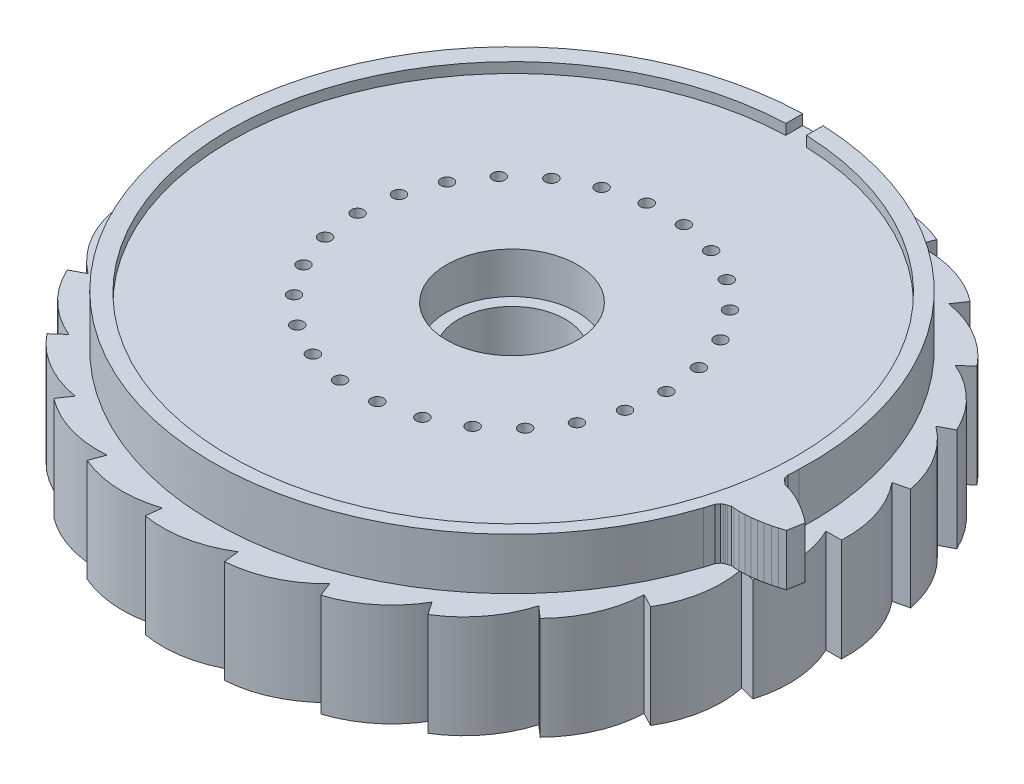
SolidWorks part; units mm, degrees
material "1060 Alloy"
ref_plane "Front Plane" through (0, 0, 0) normal (0, 0, 1) x (1, 0, 0)
ref_plane "Top Plane" through (0, 0, 0) normal (0, 1, 0) x (1, 0, 0)
ref_plane "Right Plane" through (0, 0, 0) normal (1, 0, 0) x (0, 0, -1)
sketch "Sketch1" plane through (0, 0, 0) normal (0, 1, 0) x (1, 0, 0)
  line L0 (0, 0) -> (54.8903, 0) construction
  line L1 (0, 0) -> (47.5263, 11.7142) construction
  line L2 (0, 0) -> (29.6137, 7.2991)
  line L3 (0, 0) -> (32, 0)
  circle A0 centre (0, 0) radius 32 construction
  circle A1 centre (0, 0) radius 30.5 construction
  arc A2 (29.6137, 7.2991) -> (32, 0) centre (21.3514, 0.5583) cw
  circle A3 centre (0, 0) radius 31.25 construction
  dimension "D1" = 62.5
  dimension "D2" = 1.5
  dimension "D4" = 0.75
  dimension "D3" = 13.846
extrude "Extrude ratchet edge" add sketch "Sketch1" along normal blind 10
pattern_circular "Pattern edge to form gear" count 26 over 360 about axis through (0, 0, 0) along (0, 1, 0) of "Extrude ratchet edge"
sketch "Sketch12" plane through (0, 10, 0) normal (0, 1, 0) x (1, 0, 0)
  line L0 (28.9274, -2.1257) -> (29.0264, -2.5152)
  line L1 (29.0264, -2.5152) -> (29.1427, -2.6718)
  line L2 (29.1427, -2.6718) -> (29.2623, -2.7873)
  line L3 (29.2623, -2.7873) -> (29.3837, -2.8801)
  line L4 (29.3837, -2.8801) -> (29.6242, -3.0821)
  line L5 (29.6242, -3.0821) -> (29.8792, -3.1399)
  line L6 (29.8792, -3.1399) -> (30.3843, -3.2992)
  line L7 (30.3843, -3.2992) -> (30.8844, -3.4996)
  line L8 (30.8844, -3.4996) -> (31.3799, -3.7334)
  line L9 (31.3799, -3.7334) -> (31.8708, -3.9966)
  line L10 (31.8708, -3.9966) -> (32.3568, -4.2867)
  line L11 (32.3568, -4.2867) -> (32.8378, -4.602)
  line L12 (32.8378, -4.602) -> (33.3134, -4.9413)
  line L13 (33.3134, -4.9413) -> (33.7833, -5.3035)
  line L14 (33.7833, -5.3035) -> (33.502, -6.8593)
  line L15 (33.502, -6.8593) -> (32.9351, -7.0341)
  line L16 (32.9351, -7.0341) -> (32.3708, -7.1854)
  line L17 (32.3708, -7.1854) -> (31.8099, -7.3124)
  line L18 (31.8099, -7.3124) -> (31.253, -7.414)
  line L19 (31.253, -7.414) -> (30.7011, -7.4887)
  line L20 (30.7011, -7.4887) -> (30.1551, -7.5342)
  line L21 (30.1551, -7.5342) -> (29.6165, -7.5468)
  line L22 (29.6165, -7.5468) -> (29.0876, -7.5192)
  line L23 (29.0876, -7.5192) -> (28.8285, -7.4842)
  line L24 (28.8285, -7.4842) -> (28.5325, -7.5891)
  line L25 (28.5325, -7.5891) -> (28.3863, -7.6336)
  line L26 (28.3863, -7.6336) -> (28.2339, -7.6999)
  line L27 (28.2339, -7.6999) -> (28.07, -7.8059)
  line L28 (28.07, -7.8059) -> (27.841, -8.136)
  line L29 (27.841, -8.136) -> (27.578, -8.987)
  line L779 (28.9844, -1.1053) -> (28.9274, -2.1257)
  arc A0 (27.578, -8.987) -> (28.9844, -1.1053) centre (0, 0) cw
extrude "Gear face" add sketch "Sketch12" along normal blind 5
sketch "Sketch7" plane through (0, 15, 0) normal (0, 1, 0) x (1, 0, 0)
  circle A0 centre (0, 0) radius 6.35
  dimension "D1" = 12.7
sketch "Sketch10" plane through (0, 15, 0) normal (0, 1, 0) x (1, 0, 0)
  line L0 (-0.7538, 29.3517) -> (-0.7538, 27.3517)
  line L1 (1.2462, 27.3517) -> (1.2462, 29.3517)
  line L2 (1.2462, 29.3517) -> (-0.7538, 29.3517)
  line L3 (0.2462, -0.1301) -> (0.2462, 41.1735) construction
  line L4 (0.2462, -0.1301) -> (0.2462, 36.6199) construction
  arc A0 (-0.7538, 27.3517) -> (1.2462, 27.3517) centre (0.2462, -0.1301) ccw
  dimension "D1" = 2
extrude "PCB inset" cut sketch "Sketch10" against normal blind 1
extrude "Cut bearing hole" cut sketch "Sketch7" against normal up to surface (5 mm away) up to face at (32.4022, 10, 5.8482)
sketch "Sketch11" plane through (0, 0, 0) normal (0, -1, 0) x (1, 0, 0)
  line L0 (1, -29.4818) -> (1, -27.4818)
  line L1 (-1, -27.4818) -> (-1, -29.4818)
  line L2 (-1, -29.4818) -> (1, -29.4818)
  line L3 (0, 0) -> (0, -100.666) construction
  arc A0 (1, -27.4818) -> (-1, -27.4818) centre (0, 0) ccw
  point P0 (0, -29.4818)
  dimension "D2" = 2
  dimension "D3" = 27.5
  dimension "D1" = 2
  dimension "D4" = 2
extrude "PCB inset rear" cut sketch "Sketch11" against normal blind 1
sketch "pin holes" plane through (0, 14, 0) normal (0, 1, 0) x (1, 0, 0)
  circle A0 centre (15, 0) radius 0.6
  circle A1 centre (14.5641, -3.5897) radius 0.6
  circle A2 centre (13.2818, -6.9708) radius 0.6
  circle A3 centre (11.2277, -9.9468) radius 0.6
  circle A4 centre (8.521, -12.3448) radius 0.6
  circle A5 centre (5.3191, -14.0252) radius 0.6
  circle A6 centre (1.8081, -14.8906) radius 0.6
  circle A7 centre (-1.8081, -14.8906) radius 0.6
  circle A8 centre (-5.3191, -14.0252) radius 0.6
  circle A9 centre (-8.521, -12.3448) radius 0.6
  circle A10 centre (-11.2277, -9.9468) radius 0.6
  circle A11 centre (-13.2818, -6.9708) radius 0.6
  circle A12 centre (-14.5641, -3.5897) radius 0.6
  circle A13 centre (-15, 0) radius 0.6
  circle A14 centre (-14.5641, 3.5897) radius 0.6
  circle A15 centre (-13.2818, 6.9708) radius 0.6
  circle A16 centre (-11.2277, 9.9468) radius 0.6
  circle A17 centre (-8.521, 12.3448) radius 0.6
  circle A18 centre (-5.3191, 14.0252) radius 0.6
  circle A19 centre (-1.8081, 14.8906) radius 0.6
  circle A20 centre (1.8081, 14.8906) radius 0.6
  circle A21 centre (5.3191, 14.0252) radius 0.6
  circle A22 centre (8.521, 12.3448) radius 0.6
  circle A23 centre (11.2277, 9.9468) radius 0.6
  circle A24 centre (13.2818, 6.9708) radius 0.6
  circle A25 centre (14.5641, 3.5897) radius 0.6
  point P55 (0, 0)
  dimension "D1" = 1.2
  dimension "D2" = 15
  dimension "D3" = 26
extrude "Pin holes cut" cut sketch "pin holes" against normal through all
sketch "Sketch14" [suppressed] plane through (0, 14, 0) normal (0, 1, 0) x (1, 0, 0)
  line L0 (0, 0) -> (0, 34.7764) construction
  circle A0 centre (0, 25) radius 1.5875
  circle A1 centre (21.6506, -12.5) radius 1.5875
  circle A2 centre (-21.6506, -12.5) radius 1.5875
  point P11 (0, 0)
  dimension "D1" = 3.175
  dimension "D2" = 25
  dimension "D3" = 3
extrude "Cut-Extrude2" [suppressed] cut sketch "Sketch14" against normal through all
sketch "Sketch13" [suppressed] plane through (0, 10, 0) normal (0, 1, 0) x (1, 0, 0)
  circle A0 centre (0, 0) radius 52.9385
extrude "Cut in half for 3D print" [suppressed] cut sketch "Sketch13" along normal through all
sketch "Sketch15" plane through (0, 0, 0) normal (0, -1, 0) x (1, 0, 0)
  circle A0 centre (0, 0) radius 5.18
  dimension "D1" = 10.36
extrude "Cut-Extrude3" cut sketch "Sketch15" against normal through all
equation "\"Bearing size\"= 12.7mm"
equation "\"D1@Sketch7\" = \"Bearing size\""
equation "\"dedendum\"= 2mm"
equation "\"addendum\"= 2mm"
equation "\"D5@Iteration wheel\" = \"addendum\""
equation "\"base diameter\"=58"
equation "\"alpha\"= sqr ( ( \"base diameter\" + \"dedendum\" ) ^ 2 - \"base diameter\" ^ 2 ) / \"base diameter\" * 180 / PI - \"phi\""
equation "\"phi\"= 20"
